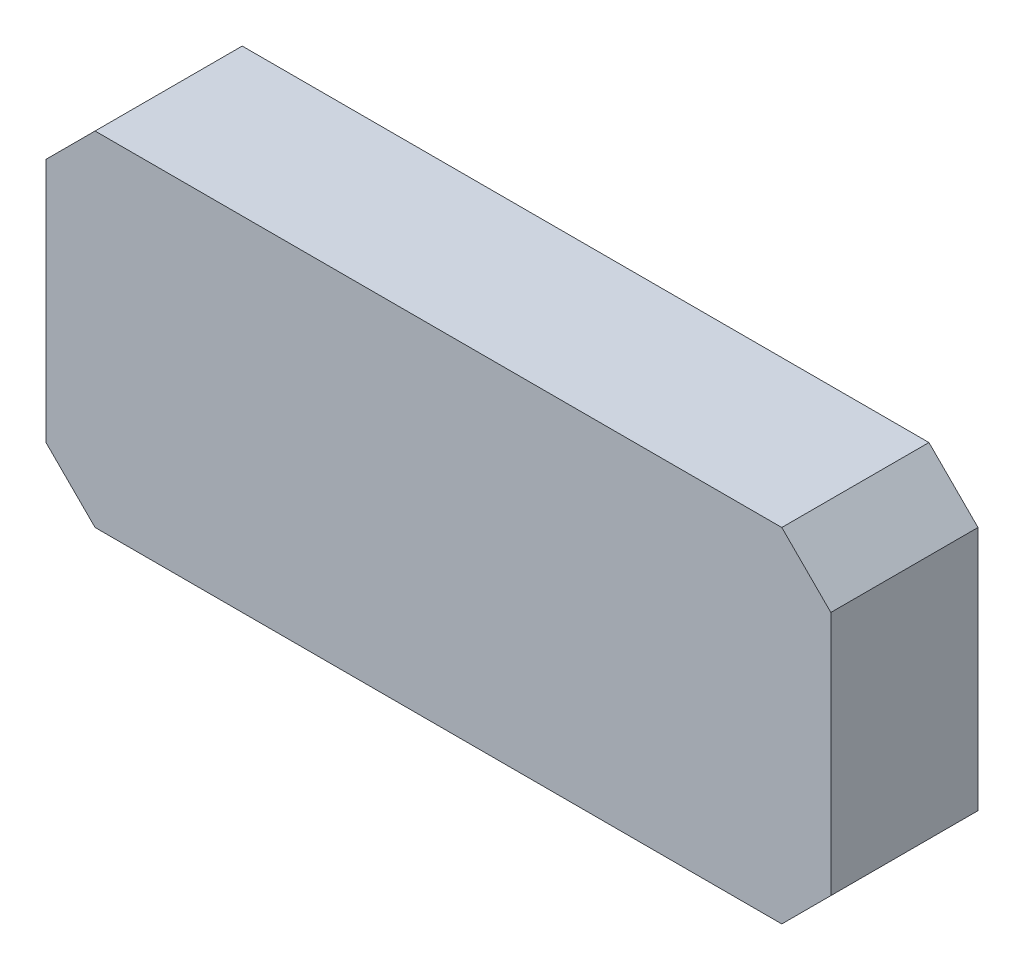
SolidWorks part; units mm, degrees
material "Стекло"
ref_plane "Front" through (0, 0, 0) normal (0, 0, 1) x (1, 0, 0)
ref_plane "Top" through (0, 0, 0) normal (0, 1, 0) x (1, 0, 0)
ref_plane "Right" through (0, 0, 0) normal (1, 0, 0) x (0, 0, -1)
sketch "Эскиз1" plane through (0, 0, 0) normal (0, 0, 1) x (1, 0, 0)
  line L1 (-8, -3) -> (8, -3)
  line L2 (-8, -3) -> (-8, 4)
  line L3 (-8, 4) -> (8, 4)
  line L4 (8, -3) -> (8, 4)
  dimension "D1" = 16
  dimension "D2" = 7
  dimension "D3" = 3
  dimension "D4" = 8
extrude "Вытянуть1" add sketch "Эскиз1" along normal blind 3
chamfer "Фаска1" [suppressed] distance 0.5 angle 45
chamfer "Фаска2" distance 1 angle 45 4 edges at (-8, -3, 1.5) (-8, 4, 1.5) (8, -3, 1.5) (8, 4, 1.5)
